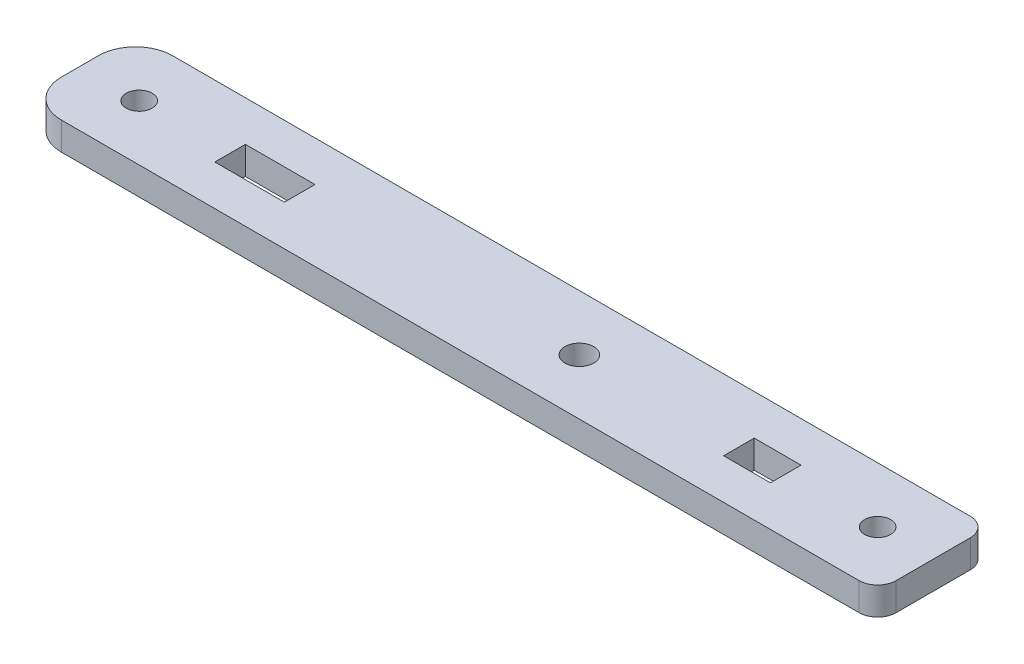
SolidWorks part; units mm, degrees
ref_plane "Front Plane" through (0, 0, 0) normal (0, 0, 1) x (1, 0, 0)
ref_plane "Top Plane" through (0, 0, 0) normal (0, 1, 0) x (1, 0, 0)
ref_plane "Right Plane" through (0, 0, 0) normal (1, 0, 0) x (0, 0, -1)
sketch "Sketch1" plane through (0, 0, 0) normal (0, 1, 0) x (1, 0, 0)
  line L1 (0, 0) -> (92, 0)
  line L2 (0, 0) -> (0, 12)
  line L3 (0, 12) -> (92, 12)
  line L4 (92, 0) -> (92, 12)
  dimension "D1" = 92
  dimension "D2" = 12
extrude "Boss-Extrude1" add sketch "Sketch1" along normal blind 3
fillet "Fillet1" radius 4 2 edges at (0, 1.5, -12) (0, 1.5, 0)
fillet "Fillet2" radius 2 2 edges at (92, 1.5, -12) (92, 1.5, 0)
sketch "Sketch2" plane through (0, 3, 0) normal (0, 1, 0) x (1, 0, 0)
  line L0 (0, 6) -> (92, 6) construction
  line L1 (16.2, 7.5) -> (23.7, 7.5)
  line L2 (16.2, 7.5) -> (16.2, 4.5)
  line L3 (16.2, 4.5) -> (23.7, 4.5)
  line L4 (23.7, 7.5) -> (23.7, 4.5)
  line L5 (71.05, 7.5) -> (76.1, 7.5)
  line L6 (71.05, 7.5) -> (71.05, 4.5)
  line L7 (71.05, 4.5) -> (76.1, 4.5)
  line L8 (76.1, 7.5) -> (76.1, 4.5)
  line L9 (0, 8) -> (0, 4) construction
  line L10 (92, 2) -> (92, 10) construction
  circle A0 centre (6.4, 6) radius 1.4
  circle A1 centre (53.85, 6) radius 1.55
  circle A2 centre (86, 6) radius 1.4
  point P14 (76.1, 6)
  point P15 (73.575, 7.5)
  point P22 (56.3125, 6)
  dimension "D1" = 2.8
  dimension "D2" = 3.1
  dimension "D3" = 3
  dimension "D4" = 5.05
  dimension "D5" = 7.5
  dimension "D6" = 6.4
  dimension "D7" = 16.2
  dimension "D8" = 6
  dimension "D9" = 15.9
  dimension "D10" = 38.15
extrude "Cut-Extrude1" cut sketch "Sketch2" against normal through all
sketch "Sketch3" plane through (0, 3, 0) normal (0, 1, 0) x (1, 0, 0)
  line L0 (71.05, 7.5) -> (71.05, 4.5) construction
  line L1 (16.2, 7.5) -> (23.7, 7.5)
  line L2 (16.2, 7.5) -> (16.2, 7.65)
  line L3 (16.2, 7.65) -> (23.7, 7.65)
  line L4 (23.7, 7.5) -> (23.7, 7.65)
  line L5 (16.2, 4.5) -> (23.7, 4.5)
  line L6 (16.2, 4.5) -> (16.2, 4.35)
  line L7 (16.2, 4.35) -> (23.7, 4.35)
  line L8 (23.7, 4.5) -> (23.7, 4.35)
  line L9 (76.1, 7.5) -> (71.05, 7.5)
  line L10 (76.1, 7.5) -> (76.1, 7.65)
  line L11 (76.1, 7.65) -> (71.05, 7.65)
  line L12 (71.05, 7.5) -> (71.05, 7.65)
  line L13 (76.1, 4.5) -> (71.05, 4.5)
  line L14 (76.1, 4.5) -> (76.1, 4.35)
  line L15 (76.1, 4.35) -> (71.05, 4.35)
  line L16 (71.05, 4.5) -> (71.05, 4.35)
  line L17 (23.7, 4.5) -> (23.7, 7.5) construction
  dimension "D1" = 0.15
extrude "Cut-Extrude2" cut sketch "Sketch3" against normal through all
